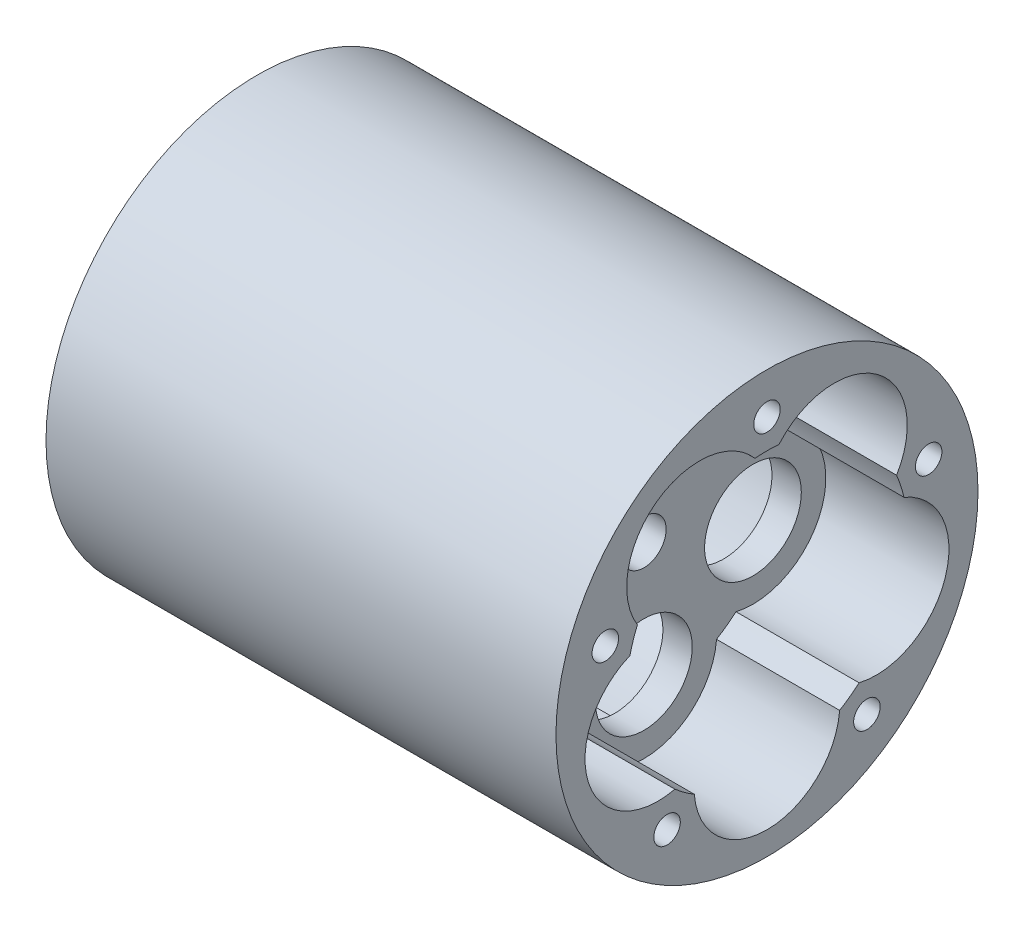
SolidWorks part; units mm, degrees
material "Acrylic (Medium-high impact)"
ref_plane "Front Plane" through (0, 0, 0) normal (0, 0, 1) x (1, 0, 0)
ref_plane "Top Plane" through (0, 0, 0) normal (0, 1, 0) x (1, 0, 0)
ref_plane "Right Plane" through (0, 0, 0) normal (1, 0, 0) x (0, 0, -1)
sketch "Sketch1" plane through (0, 0, 0) normal (1, 0, 0) x (0, 0, -1)
  line L0 (0, 0) -> (5.75, 7.9142) construction
  line L2 (9.3037, -3.023) -> (0, 0) construction
  line L3 (0, 0) -> (0, -9.7825) construction
  line L5 (-9.3037, -3.023) -> (0, 0) construction
  line L6 (-5.75, 7.9142) -> (0, 0) construction
  circle A0 centre (0, 0) radius 9.7825 construction
  circle A1 centre (-5.75, 7.9142) radius 5.75 construction
  circle A2 centre (5.75, 7.9142) radius 5.75 construction
  circle A3 centre (9.3037, -3.023) radius 5.75 construction
  circle A4 centre (0, -9.7825) radius 5.75 construction
  circle A5 centre (-9.3037, -3.023) radius 5.75 construction
  circle A6 centre (-5.75, 7.9142) radius 4.125
  circle A7 centre (5.75, 7.9142) radius 4.125
  circle A8 centre (9.3037, -3.023) radius 4.125
  circle A9 centre (0, -9.7825) radius 4.125
  circle A10 centre (-9.3037, -3.023) radius 4.125
  circle A11 centre (0, 0) radius 16
  dimension "D1" = 11.5
  dimension "D2" = 8.25
  dimension "D8" = 32
  dimension "D4" = 72
  dimension "D5" = 72
  dimension "D6" = 72
  dimension "D7" = 72
extrude "Boss-Extrude1" add sketch "Sketch1" along normal blind 2.5
sketch "Sketch2" plane through (2.5, 0, 0) normal (1, 0, 0) x (0, 0, -1)
  circle A0 centre (0, 0) radius 16
  circle A1 centre (0, 0) radius 18
  dimension "D1" = 32
  dimension "D2" = 36
extrude "Boss-Extrude2" add sketch "Sketch2" along normal blind 10.5 and the other way blind 30
sketch "Sketch3" plane through (-27.5, 0, 0) normal (-1, 0, 0) x (0, 0, 1)
  circle A0 centre (0, 0) radius 18
  dimension "D1" = 36
extrude "Boss-Extrude3" add sketch "Sketch3" along normal blind 3
sketch "Sketch4" plane through (2.5, 0, 0) normal (1, 0, 0) x (0, 0, -1)
  circle A0 centre (0, 0) radius 1.8986
  dimension "D1" = 3.7973
extrude "Cut-Extrude1" cut sketch "Sketch4" against normal blind 3
sketch "Sketch5" plane through (2.5, 0, 0) normal (1, 0, 0) x (0, 0, -1)
  line L0 (-0.75, -15) -> (-0.5, -14.75)
  line L1 (-0.75, -16.25) -> (0.75, -16.25)
  line L2 (-0.75, -16.25) -> (-0.75, -15)
  line L3 (-0.5, -14.75) -> (0.5, -14.75)
  line L4 (0.75, -16.25) -> (0.75, -15)
  line L5 (0.5, -14.75) -> (0.75, -15)
  point P1 (0.75, -14.75)
  point P2 (-0.75, -14.75)
  point P9 (0.5, -15.4985)
  point P10 (-0.5, -15.437)
  dimension "D1" = 14.75
  dimension "D2" = 1.5
  dimension "D3" = 1.5
  dimension "D4" = 0.75
  dimension "D5" = 0.25
  dimension "D6" = 0.25
extrude "Boss-Extrude4" add sketch "Sketch5" against normal blind 31
sketch "Sketch6" plane through (2.5, 0, 0) normal (1, 0, 0) x (0, 0, -1)
  line L0 (-3.2328, -4.4496) -> (0, 0) construction
  line L1 (0, 0) -> (3.2328, -4.4496) construction
  line L2 (0, 0) -> (0, 16) construction
  line L3 (5.2308, 1.6996) -> (0, 0) construction
  circle A0 centre (3.2328, -4.4496) radius 0.75 construction
  circle A1 centre (5.2308, 1.6996) radius 0.75 construction
  circle A2 centre (-3.2328, -4.4496) radius 0.75 construction
  circle A3 centre (0, 0) radius 16 construction
  circle A4 centre (0, 5.5) radius 0.75
  dimension "D5" = 1.5
  dimension "D6" = 1.5
  dimension "D1" = 5.5
  dimension "D2" = 72
  dimension "D3" = 72
  dimension "D4" = 72
  dimension "D7" = 5.5
extrude "Cut-Extrude2" cut sketch "Sketch6" against normal blind 3
sketch "Sketch7" plane through (2.5, 0, 0) normal (1, 0, 0) x (0, 0, -1)
  arc A0 (-1.0255, 11.9561) -> (-11.054, 4.67) centre (-5.75, 7.9142) ccw
  arc A1 (11.054, 4.67) -> (1.0255, 11.9561) centre (5.75, 7.9142) ccw
  arc A2 (7.8573, -9.0699) -> (11.6878, 2.7193) centre (9.3037, -3.023) ccw
  arc A3 (-6.1979, -10.2755) -> (6.1979, -10.2755) centre (0, -9.7825) ccw
  arc A4 (-11.6878, 2.7193) -> (-7.8573, -9.0699) centre (-9.3037, -3.023) ccw
  arc A5 (-11.054, 4.67) -> (-11.6878, 2.7193) centre (0, 0) ccw
  arc A6 (-7.8573, -9.0699) -> (-6.1979, -10.2755) centre (0, 0) ccw
  arc A7 (6.1979, -10.2755) -> (7.8573, -9.0699) centre (0, 0) ccw
  arc A8 (11.6878, 2.7193) -> (11.054, 4.67) centre (0, 0) ccw
  arc A9 (1.0255, 11.9561) -> (-1.0255, 11.9561) centre (0, 0) ccw
  circle A10 centre (0, 0) radius 16
  circle M2 centre (0, 0) radius 16
  dimension "D1" = 24
  dimension "D2" = 6.2175
  dimension "D3" = 32
extrude "Boss-Extrude5" add sketch "Sketch7" along normal up to surface (10.5 mm away) contours A9 A1 A0 M2 | A5 A0 A4 M2 | A6 A4 A3 M2 | A7 A3 A2 M2 | A8 A2 A1 M2 up to face at (13, 0, -18)
sketch "Sketch8" plane through (13, 0, 0) normal (1, 0, 0) x (0, 0, -1)
  line L0 (0, 14.5) -> (0, 0) construction
  line L1 (0, 0) -> (13.7903, 4.4807) construction
  line L3 (8.5229, -11.7307) -> (0, 0) construction
  line L4 (0, 0) -> (-8.5229, -11.7307) construction
  line L6 (-13.7903, 4.4807) -> (0, 0) construction
  circle A0 centre (0, 0) radius 14.5 construction
  circle A1 centre (0, 14.5) radius 1.1303
  circle A2 centre (13.7903, 4.4807) radius 1.1303
  circle A3 centre (8.5229, -11.7307) radius 1.1303
  circle A4 centre (-8.5229, -11.7307) radius 1.1303
  circle A5 centre (-13.7903, 4.4807) radius 1.1303
  dimension "D1" = 2.2606
  dimension "D6" = 29
  dimension "D2" = 72
  dimension "D3" = 72
  dimension "D4" = 72
  dimension "D5" = 72
extrude "Cut-Extrude3" cut sketch "Sketch8" against normal blind 23
